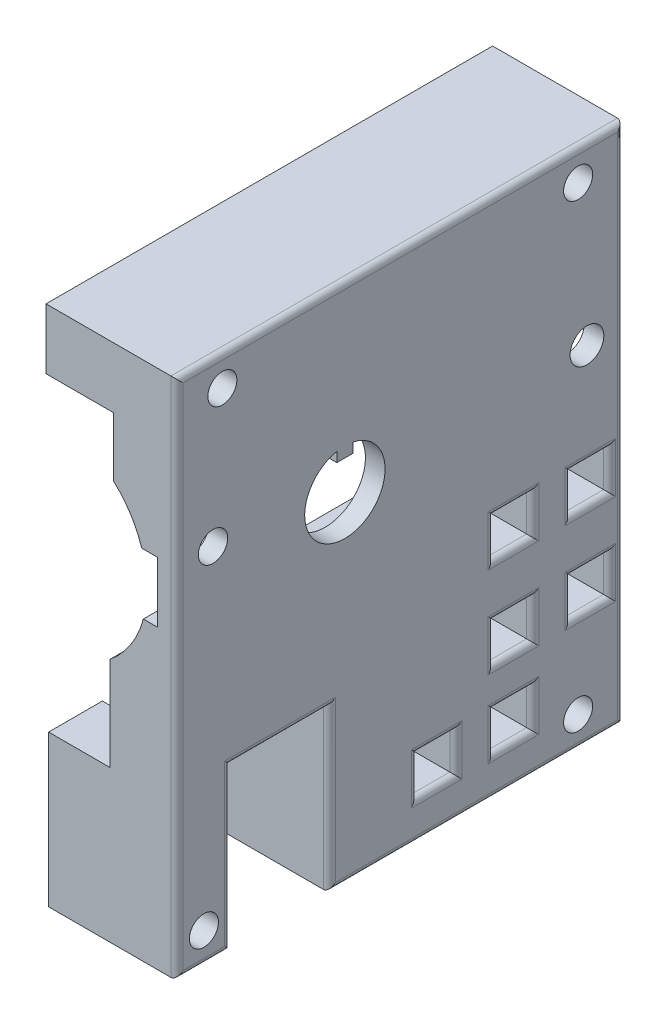
SolidWorks part; units mm, degrees
ref_plane "Front" through (0, 0, 0) normal (0, 0, 1) x (1, 0, 0)
ref_plane "Top" through (0, 0, 0) normal (0, 1, 0) x (1, 0, 0)
ref_plane "Right" through (0, 0, 0) normal (1, 0, 0) x (0, 0, -1)
sketch "Profile" plane through (0, 0, 0) normal (0, 0, 1) x (1, 0, 0)
  line L0 (-6.0107, -58.6279) -> (-6.0107, -33.6279)
  line L1 (-6.0107, -58.6279) -> (15.1893, -58.6279)
  line L2 (-6.4407, 17.4121) -> (-6.4407, 27.4121)
  line L3 (-6.4407, 27.4121) -> (15.1893, 27.4121)
  line L4 (15.1893, -58.6279) -> (15.1893, 27.4121)
  line L5 (-6.0107, -33.6279) -> (4.1393, -33.6279)
  line L6 (4.1393, -33.6279) -> (4.1393, -18.1379)
  line L7 (9.6313, -9.6379) -> (11.9493, -9.6379)
  line L8 (11.9493, -9.6379) -> (11.9493, 0.3621)
  line L9 (9.3593, 0.3621) -> (11.9493, 0.3621)
  line L10 (4.7093, 17.4121) -> (4.7093, 7.6371)
  line L11 (4.7093, 17.4121) -> (-6.4407, 17.4121)
  arc A0 (9.3593, 0.3621) -> (4.7093, 7.6371) centre (-6.1754, -4.4437) ccw
  arc A1 (4.1393, -18.1379) -> (9.6313, -9.6379) centre (-6.0948, -5.5013) ccw
  dimension "D14" = 16.261
  dimension "D17" = 16.261
  dimension "D2" = 10
  dimension "D3" = 2.59
  dimension "D4" = 2.318
  dimension "D5" = 9.775
  dimension "D6" = 11.15
  dimension "D7" = 15.49
  dimension "D8" = 10.15
  dimension "D9" = 25
  dimension "D10" = 21.2
  dimension "D11" = 86.04
  dimension "D12" = 21.63
  dimension "D13" = 10
  dimension "D15" = 23.99
  dimension "D16" = 5.492
extrude "ProfileExtrude" add sketch "Profile" along normal blind 73.76
sketch "HoseWindow" plane through (15.1893, 0, 0) normal (1, 0, 0) x (0, 0, -1)
  line L0 (-73.76, -58.6279) -> (0, -58.6279) construction
  line L1 (-64.87, -58.6279) -> (-48.58, -58.6279)
  line L2 (-64.87, -58.6279) -> (-64.87, -32.1279)
  line L3 (-64.87, -32.1279) -> (-48.58, -32.1279)
  line L4 (-48.58, -58.6279) -> (-48.58, -32.1279)
  line L5 (-73.76, -58.6279) -> (-73.76, 27.4121) construction
  dimension "D1" = 16.29
  dimension "D2" = 26.5
  dimension "D3" = 8.89
extrude "HoseWindowCut" cut sketch "HoseWindow" against normal through all
sketch "CageScrews" plane through (15.1893, 0, 0) normal (1, 0, 0) x (0, 0, -1)
  line L0 (-73.76, 27.4121) -> (0, 27.4121) construction
  line L1 (-73.76, -58.6279) -> (-73.76, 27.4121) construction
  line L2 (0, -58.6279) -> (0, 27.4121) construction
  line L3 (-48.58, -58.6279) -> (0, -58.6279) construction
  line L4 (-73.76, -58.6279) -> (-64.87, -58.6279) construction
  circle A0 centre (-66.26, 22.4121) radius 2.4
  circle A1 centre (-7.5, 22.4121) radius 2.4
  circle A2 centre (-7.5, -53.6279) radius 2.4
  circle A3 centre (-69.31, -53.6279) radius 2.4
  dimension "D1" = 4.8
  dimension "D2" = 4.8
  dimension "D3" = 4.8
  dimension "D4" = 4.8
  dimension "D5" = 5
  dimension "D6" = 7.5
  dimension "D7" = 7.5
  dimension "D8" = 5
  dimension "D9" = 5
  dimension "D10" = 7.5
  dimension "D11" = 5
  dimension "D12" = 4.45
extrude "CageScrewsCut" cut sketch "CageScrews" against normal through all
sketch "AxleHole" plane through (15.1893, 0, 0) normal (1, 0, 0) x (0, 0, -1)
  line L0 (-46.03, 2.3073) -> (-46.03, -9.2169) construction
  line L1 (-44.699, 2.3073) -> (-47.361, 2.3073)
  line L2 (-47.361, 2.3073) -> (-47.361, 3.9263)
  line L3 (-44.699, 2.3073) -> (-44.699, 3.9263)
  line L4 (-48.58, -58.6279) -> (0, -58.6279) construction
  line L5 (0, -58.6279) -> (0, 27.4121) construction
  arc A0 (-47.361, 3.9263) -> (-44.699, 3.9263) centre (-46.03, -2.5779) ccw
  dimension "D1" = 13.278
  dimension "D2" = 1.619
  dimension "D3" = 1.619
  dimension "D4" = 1.331
  dimension "D5" = 56.05
  dimension "D6" = 46.03
extrude "AxleHoleCut" cut sketch "AxleHole" against normal through all
sketch "SetScrews" plane through (15.1893, 0, 0) normal (1, 0, 0) x (0, 0, -1)
  line L0 (-46.03, -9.2169) -> (-46.03, -2.5779) construction
  circle A0 centre (-67.8072, 0.5449) radius 2.4263
  circle A1 centre (-6.043, -1.5582) radius 2.7888
  arc A3 (-47.361, 3.9263) -> (-44.699, 3.9263) centre (-46.03, -2.5779) ccw construction
  dimension "D1" = 22
  dimension "D2" = 40
extrude "SetScrewsCut" cut sketch "SetScrews" against normal through all
sketch "Sketch1" plane through (15.1893, 0, 0) normal (1, 0, 0) x (0, 0, -1)
  line L0 (-21.35, -45.9279) -> (-21.35, -52.2779)
  line L1 (-21.35, -45.9279) -> (-15, -45.9279)
  line L2 (-21.35, -52.2779) -> (-15, -52.2779)
  line L3 (-15, -45.9279) -> (-15, -52.2779)
  line L4 (0, -58.6279) -> (0, 27.4121) construction
  line L5 (-48.58, -58.6279) -> (0, -58.6279) construction
  line L6 (-34.05, -45.9279) -> (-34.05, -52.2779)
  line L7 (-34.05, -45.9279) -> (-27.7, -45.9279)
  line L8 (-34.05, -52.2779) -> (-27.7, -52.2779)
  line L9 (-27.7, -45.9279) -> (-27.7, -52.2779)
  line L10 (-8.65, -33.2279) -> (-8.65, -39.5779)
  line L11 (-8.65, -33.2279) -> (-2.3, -33.2279)
  line L12 (-8.65, -39.5779) -> (-2.3, -39.5779)
  line L13 (-2.3, -33.2279) -> (-2.3, -39.5779)
  line L14 (-21.35, -33.2279) -> (-21.35, -39.5779)
  line L15 (-21.35, -33.2279) -> (-15, -33.2279)
  line L16 (-21.35, -39.5779) -> (-15, -39.5779)
  line L17 (-15, -33.2279) -> (-15, -39.5779)
  line L18 (-34.05, -33.2279) -> (-34.05, -39.5779) [skipped]
  line L19 (-34.05, -33.2279) -> (-27.7, -33.2279) [skipped]
  line L20 (-34.05, -39.5779) -> (-27.7, -39.5779) [skipped]
  line L21 (-27.7, -33.2279) -> (-27.7, -39.5779) [skipped]
  line L22 (-8.65, -18.2279) -> (-8.65, -24.5779)
  line L23 (-8.65, -18.2279) -> (-2.3, -18.2279)
  line L24 (-8.65, -24.5779) -> (-2.3, -24.5779)
  line L25 (-2.3, -18.2279) -> (-2.3, -24.5779)
  line L26 (-21.35, -18.2279) -> (-21.35, -24.5779)
  line L27 (-21.35, -18.2279) -> (-15, -18.2279)
  line L28 (-21.35, -24.5779) -> (-15, -24.5779)
  line L29 (-15, -18.2279) -> (-15, -24.5779)
  dimension "D1" = 15
  dimension "D2" = 6.35
  dimension "D3" = 6.35
  dimension "D4" = 6.35
  dimension "D5" = 2
  dimension "D6" = 2
  dimension "D7" = 2
  dimension "D8" = 2
extrude "Cut-Extrude1" cut sketch "Sketch1" against normal through all
fillet "Fillet1" radius 1 32 edges at (15.1893, -52.2779, 30.875) (15.1893, -49.1029, 34.05) (15.1893, -45.9279, 30.875) (15.1893, -49.1029, 27.7) (15.1893, -49.1029, 21.35) (15.1893, -52.2779, 18.175) (15.1893, -49.1029, 15) (15.1893, -45.9279, 18.175) (15.1893, -36.4029, 8.65) (15.1893, -39.5779, 5.475) (15.1893, -36.4029, 2.3) (15.1893, -33.2279, 5.475) (15.1893, -36.4029, 21.35) (15.1893, -39.5779, 18.175) (15.1893, -36.4029, 15) (15.1893, -33.2279, 18.175) (15.1893, -21.4029, 21.35) (15.1893, -24.5779, 18.175) (15.1893, -21.4029, 15) (15.1893, -18.2279, 18.175) (15.1893, -21.4029, 8.65) (15.1893, -24.5779, 5.475) (15.1893, -21.4029, 2.3) (15.1893, -18.2279, 5.475) (15.1893, -58.6279, 69.315) (15.1893, -45.3779, 64.87) (15.1893, -32.1279, 56.725) (15.1893, -45.3779, 48.58) (15.1893, -58.6279, 24.29) (15.1893, -15.6079, 0) (15.1893, 27.4121, 36.88) (15.1893, -15.6079, 73.76)
equation "\"BottomEdge\"=21.20mm"
equation "\"TopEdge\"=21.63mm"
equation "\"TotalHeight\"=86.04mm"
equation "\"TotalLength\"=73.76mm"
equation "\"Screw Clearance\" = 10mm"
equation "\"TopDepth\"= 11.15mm"
equation "\"BottomDepth\"=10.15mm"
equation "\"TopHeight\"=9.775mm"
equation "\"BottomHeight\"=15.49mm"
equation "\"TopChannelDepth\"=2.59mm"
equation "\"BottomChannelDepth\"=2.318mm"
equation "\"ChannelHeight\"=10mm"
equation "\"ChamberRadius\"=16.261mm"
equation "\"ChanRelHeight\"=23.99mm"
equation "\"ChanRelDepth\"=5.492mm"
equation "\"D2@Profile\"= \"ChannelHeight\""
equation "\"D4@Profile\"= \"BottomChannelDepth\""
equation "\"D3@Profile\"= \"TopChannelDepth\""
equation "\"D5@Profile\"= \"TopHeight\""
equation "\"D7@Profile\"= \"BottomHeight\""
equation "\"ScrewClearanceBottom\" = 25mm"
equation "\"D9@Profile\"=\"ScrewClearanceBottom\""
equation "\"D13@Profile\"= \"Screw Clearance\""
equation "\"D8@Profile\"= \"BottomDepth\""
equation "\"D6@Profile\"= \"TopDepth\""
equation "\"D10@Profile\"= \"BottomEdge\""
equation "\"D12@Profile\"= \"TopEdge\""
equation "\"D11@Profile\"= \"TotalHeight\""
equation "\"D15@Profile\"= \"ChanRelHeight\""
equation "\"D16@Profile\"= \"ChanRelDepth\""
equation "\"D17@Profile\"= \"ChamberRadius\""
equation "\"D14@Profile\"= \"ChamberRadius\""
equation "\"D1@ProfileExtrude\"= \"TotalLength\""
equation "\"CageScrewDiameter\"=4.8mm"
equation "\"SetScrewDiameter\"=3.5mm"
equation "\"AxleRadius\"=6.639mm"
equation "\"KeyHeight\"=1.619mm"
equation "\"KeyWidth\"=2.662mm"
equation "\"HoseWindowWidth\"=16.29mm"
equation "\"HoseWindowHeight\"=26.5mm"
equation "\"HoseWindow-Edge\"=8.89mm"
equation "\"CageScrew-VerticalEdge\"=5.0mm"
equation "\"CageScrew-HorizontalEdge\"=7.5mm"
equation "\"CageScrew-HoseCornerScrewEdge\"=4.45mm"
equation "\"Axle-BottomEdge\"=56.05mm"
equation "\"Axle-FrontEdge\"=46.03mm"
equation "\"FrontSetScrew-Axel\"=40mm"
equation "\"D1@HoseWindow\"= \"HoseWindowWidth\""
equation "\"D2@HoseWindow\"= \"HoseWindowHeight\""
equation "\"D3@HoseWindow\"= \"HoseWindow-Edge\""
equation "\"D6@CageScrews\"= \"CageScrew-HorizontalEdge\""
equation "\"D7@CageScrews\"= \"CageScrew-HorizontalEdge\""
equation "\"D10@CageScrews\"= \"CageScrew-HorizontalEdge\""
equation "\"D12@CageScrews\"= \"CageScrew-HoseCornerScrewEdge\""
equation "\"D5@CageScrews\"= \"CageScrew-VerticalEdge\""
equation "\"D8@CageScrews\"= \"CageScrew-VerticalEdge\""
equation "\"D11@CageScrews\"= \"CageScrew-VerticalEdge\""
equation "\"D9@CageScrews\"= \"CageScrew-VerticalEdge\""
equation "\"D1@CageScrews\"= \"CageScrewDiameter\""
equation "\"D2@CageScrews\"= \"CageScrewDiameter\""
equation "\"D4@CageScrews\"= \"CageScrewDiameter\""
equation "\"D3@CageScrews\"= \"CageScrewDiameter\""
equation "\"D1@AxleHole\"= \"AxleRadius\" * 2"
equation "\"D3@AxleHole\"= \"KeyHeight\""
equation "\"D2@AxleHole\"= \"KeyHeight\""
equation "\"D4@AxleHole\"= \"KeyWidth\" / 2"
equation "\"D6@AxleHole\"= \"Axle-FrontEdge\""
equation "\"D5@AxleHole\"= \"Axle-BottomEdge\""
equation "\"D2@SetScrews\"= \"FrontSetScrew-Axel\""
equation "\"BackSetScrew-Axel\"=22mm"
equation "\"D1@SetScrews\"= \"BackSetScrew-Axel\""
equation "\"SlotFront\"=15mm"
equation "\"D1@Sketch1\"=\"SlotFront\""
equation "\"Slot\"=6.35mm"
equation "\"D2@Sketch1\"=\"Slot\""
equation "\"D3@Sketch1\"=\"Slot\""
equation "\"SlotBottom\"=6.35mm"
equation "\"D4@Sketch1\"=\"SlotBottom\""
